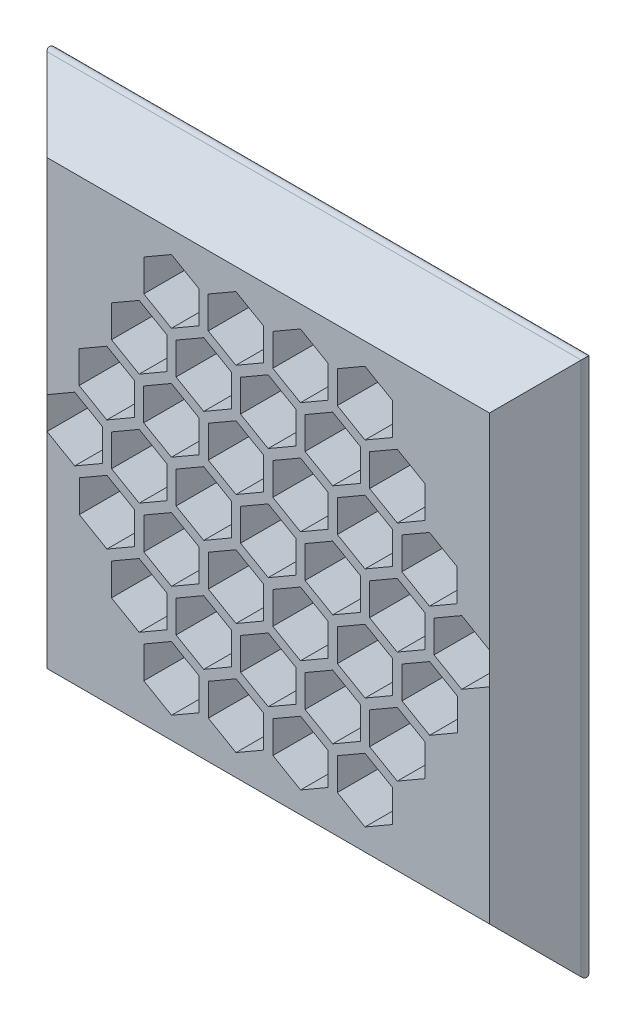
SolidWorks part; units mm, degrees
ref_plane "Front Plane" through (0, 0, 0) normal (0, 0, 1) x (1, 0, 0)
ref_plane "Top Plane" through (0, 0, 0) normal (0, 1, 0) x (1, 0, 0)
ref_plane "Right Plane" through (0, 0, 0) normal (1, 0, 0) x (0, 0, -1)
sketch "Sketch1" plane through (0, 0, 0) normal (0, 0, 1) x (1, 0, 0)
  line L1 (-50, -50) -> (50, -50)
  line L2 (-50, -50) -> (-50, 50)
  line L3 (-50, 50) -> (50, 50)
  line L4 (50, -50) -> (50, 50)
  line L5 (-50, -50) -> (50, 50) construction
  line L6 (-50, 50) -> (50, -50) construction
  point P0 (0, 0)
extrude "Boss-Extrude1" add sketch "Sketch1" along normal blind 10 draft 45
fillet "Fillet1" radius 1 4 edges at (0, 50, 0) (-50, 0, 0) (0, -50, 0) (50, 0, 0)
sketch "Sketch3" plane through (0, 0, 0) normal (0, 0, -1) x (-1, 0, 0)
  line L7 (-35, -35) -> (35, -35) construction
  line L8 (-35, -35) -> (-35, 35) construction
  line L9 (-35, 35) -> (35, 35) construction
  line L10 (35, -35) -> (35, 35) construction
  line L11 (-35, -35) -> (35, 35) construction
  line L12 (-35, 35) -> (35, -35) construction
  line L66 (11.66, -5.7735) -> (16.66, -2.8868)
  line L67 (0, -5.7735) -> (5, -2.8868)
  line L68 (5, -2.8868) -> (5, 2.8868)
  line L69 (5, 2.8868) -> (0, 5.7735)
  line L70 (0, 5.7735) -> (-5, 2.8868)
  line L71 (-5, 2.8868) -> (-5, -2.8868)
  line L72 (-5, -2.8868) -> (0, -5.7735)
  line L73 (16.66, -2.8868) -> (16.66, 2.8868)
  line L74 (16.66, 2.8868) -> (11.66, 5.7735)
  line L75 (11.66, 5.7735) -> (6.66, 2.8868)
  line L76 (6.66, 2.8868) -> (6.66, -2.8868)
  line L77 (6.66, -2.8868) -> (11.66, -5.7735)
  line L78 (23.32, -5.7735) -> (28.32, -2.8868)
  line L79 (28.32, -2.8868) -> (28.32, 2.8868)
  line L80 (28.32, 2.8868) -> (23.32, 5.7735)
  line L81 (23.32, 5.7735) -> (18.32, 2.8868)
  line L82 (18.32, 2.8868) -> (18.32, -2.8868)
  line L83 (18.32, -2.8868) -> (23.32, -5.7735)
  line L84 (34.98, -5.7735) -> (39.98, -2.8868)
  line L85 (39.98, -2.8868) -> (39.98, 2.8868)
  line L86 (39.98, 2.8868) -> (34.98, 5.7735)
  line L87 (34.98, 5.7735) -> (29.98, 2.8868)
  line L88 (29.98, 2.8868) -> (29.98, -2.8868)
  line L89 (29.98, -2.8868) -> (34.98, -5.7735)
  line L90 (-5, -2.8868) -> (0, -5.7735)
  line L91 (0, -5.7735) -> (5, -2.8868)
  line L92 (5, -2.8868) -> (5, 2.8868)
  line L93 (5, 2.8868) -> (0, 5.7735)
  line L94 (0, 5.7735) -> (-5, 2.8868)
  line L95 (-5, 2.8868) -> (-5, -2.8868)
  line L96 (0.83, -12.9846) -> (5.83, -15.8714)
  line L97 (5.83, -15.8714) -> (10.83, -12.9846)
  line L98 (10.83, -12.9846) -> (10.83, -7.2111)
  line L99 (10.83, -7.2111) -> (5.83, -4.3244)
  line L100 (5.83, -4.3244) -> (0.83, -7.2111)
  line L101 (0.83, -7.2111) -> (0.83, -12.9846)
  line L102 (6.66, -23.0825) -> (11.66, -25.9692)
  line L103 (11.66, -25.9692) -> (16.66, -23.0825)
  line L104 (16.66, -23.0825) -> (16.66, -17.309)
  line L105 (16.66, -17.309) -> (11.66, -14.4222)
  line L106 (11.66, -14.4222) -> (6.66, -17.309)
  line L107 (6.66, -17.309) -> (6.66, -23.0825)
  line L108 (12.49, -33.1803) -> (17.49, -36.0671)
  line L109 (17.49, -36.0671) -> (22.49, -33.1803)
  line L110 (22.49, -33.1803) -> (22.49, -27.4068)
  line L111 (22.49, -27.4068) -> (17.49, -24.5201)
  line L112 (17.49, -24.5201) -> (12.49, -27.4068)
  line L113 (12.49, -27.4068) -> (12.49, -33.1803)
  line L114 (-5, 2.8868) -> (-5, -2.8868)
  line L115 (-5, -2.8868) -> (0, -5.7735)
  line L116 (0, -5.7735) -> (5, -2.8868)
  line L117 (5, -2.8868) -> (5, 2.8868)
  line L118 (5, 2.8868) -> (0, 5.7735)
  line L119 (0, 5.7735) -> (-5, 2.8868)
  line L120 (-10.83, -7.2111) -> (-10.83, -12.9846)
  line L121 (-10.83, -12.9846) -> (-5.83, -15.8714)
  line L122 (-5.83, -15.8714) -> (-0.83, -12.9846)
  line L123 (-0.83, -12.9846) -> (-0.83, -7.2111)
  line L124 (-0.83, -7.2111) -> (-5.83, -4.3244)
  line L125 (-5.83, -4.3244) -> (-10.83, -7.2111)
  line L126 (-16.66, -17.309) -> (-16.66, -23.0825)
  line L127 (-16.66, -23.0825) -> (-11.66, -25.9692)
  line L128 (-11.66, -25.9692) -> (-6.66, -23.0825)
  line L129 (-6.66, -23.0825) -> (-6.66, -17.309)
  line L130 (-6.66, -17.309) -> (-11.66, -14.4222)
  line L131 (-11.66, -14.4222) -> (-16.66, -17.309)
  line L132 (-22.49, -27.4068) -> (-22.49, -33.1803)
  line L133 (-22.49, -33.1803) -> (-17.49, -36.0671)
  line L134 (-17.49, -36.0671) -> (-12.49, -33.1803)
  line L135 (-12.49, -33.1803) -> (-12.49, -27.4068)
  line L136 (-12.49, -27.4068) -> (-17.49, -24.5201)
  line L137 (-17.49, -24.5201) -> (-22.49, -27.4068)
  line L138 (0, 5.7735) -> (-5, 2.8868)
  line L139 (-5, 2.8868) -> (-5, -2.8868)
  line L140 (-5, -2.8868) -> (0, -5.7735)
  line L141 (0, -5.7735) -> (5, -2.8868)
  line L142 (5, -2.8868) -> (5, 2.8868)
  line L143 (5, 2.8868) -> (0, 5.7735)
  line L144 (-11.66, 5.7735) -> (-16.66, 2.8868)
  line L145 (-16.66, 2.8868) -> (-16.66, -2.8868)
  line L146 (-16.66, -2.8868) -> (-11.66, -5.7735)
  line L147 (-11.66, -5.7735) -> (-6.66, -2.8868)
  line L148 (-6.66, -2.8868) -> (-6.66, 2.8868)
  line L149 (-6.66, 2.8868) -> (-11.66, 5.7735)
  line L150 (-23.32, 5.7735) -> (-28.32, 2.8868)
  line L151 (-28.32, 2.8868) -> (-28.32, -2.8868)
  line L152 (-28.32, -2.8868) -> (-23.32, -5.7735)
  line L153 (-23.32, -5.7735) -> (-18.32, -2.8868)
  line L154 (-18.32, -2.8868) -> (-18.32, 2.8868)
  line L155 (-18.32, 2.8868) -> (-23.32, 5.7735)
  line L156 (-34.98, 5.7735) -> (-39.98, 2.8868)
  line L157 (-39.98, 2.8868) -> (-39.98, -2.8868)
  line L158 (-39.98, -2.8868) -> (-34.98, -5.7735)
  line L159 (-34.98, -5.7735) -> (-29.98, -2.8868)
  line L160 (-29.98, -2.8868) -> (-29.98, 2.8868)
  line L161 (-29.98, 2.8868) -> (-34.98, 5.7735)
  line L162 (5, 2.8868) -> (0, 5.7735)
  line L163 (0, 5.7735) -> (-5, 2.8868)
  line L164 (-5, 2.8868) -> (-5, -2.8868)
  line L165 (-5, -2.8868) -> (0, -5.7735)
  line L166 (0, -5.7735) -> (5, -2.8868)
  line L167 (5, -2.8868) -> (5, 2.8868)
  line L168 (-0.83, 12.9846) -> (-5.83, 15.8714)
  line L169 (-5.83, 15.8714) -> (-10.83, 12.9846)
  line L170 (-10.83, 12.9846) -> (-10.83, 7.2111)
  line L171 (-10.83, 7.2111) -> (-5.83, 4.3244)
  line L172 (-5.83, 4.3244) -> (-0.83, 7.2111)
  line L173 (-0.83, 7.2111) -> (-0.83, 12.9846)
  line L174 (-6.66, 23.0825) -> (-11.66, 25.9692)
  line L175 (-11.66, 25.9692) -> (-16.66, 23.0825)
  line L176 (-16.66, 23.0825) -> (-16.66, 17.309)
  line L177 (-16.66, 17.309) -> (-11.66, 14.4222)
  line L178 (-11.66, 14.4222) -> (-6.66, 17.309)
  line L179 (-6.66, 17.309) -> (-6.66, 23.0825)
  line L180 (-12.49, 33.1803) -> (-17.49, 36.0671)
  line L181 (-17.49, 36.0671) -> (-22.49, 33.1803)
  line L182 (-22.49, 33.1803) -> (-22.49, 27.4068)
  line L183 (-22.49, 27.4068) -> (-17.49, 24.5201)
  line L184 (-17.49, 24.5201) -> (-12.49, 27.4068)
  line L185 (-12.49, 27.4068) -> (-12.49, 33.1803)
  line L186 (5, -2.8868) -> (5, 2.8868)
  line L187 (5, 2.8868) -> (0, 5.7735)
  line L188 (0, 5.7735) -> (-5, 2.8868)
  line L189 (-5, 2.8868) -> (-5, -2.8868)
  line L190 (-5, -2.8868) -> (0, -5.7735)
  line L191 (0, -5.7735) -> (5, -2.8868)
  line L192 (10.83, 7.2111) -> (10.83, 12.9846)
  line L193 (10.83, 12.9846) -> (5.83, 15.8714)
  line L194 (5.83, 15.8714) -> (0.83, 12.9846)
  line L195 (0.83, 12.9846) -> (0.83, 7.2111)
  line L196 (0.83, 7.2111) -> (5.83, 4.3244)
  line L197 (5.83, 4.3244) -> (10.83, 7.2111)
  line L198 (16.66, 17.309) -> (16.66, 23.0825)
  line L199 (16.66, 23.0825) -> (11.66, 25.9692)
  line L200 (11.66, 25.9692) -> (6.66, 23.0825)
  line L201 (6.66, 23.0825) -> (6.66, 17.309)
  line L202 (6.66, 17.309) -> (11.66, 14.4222)
  line L203 (11.66, 14.4222) -> (16.66, 17.309)
  line L204 (22.49, 27.4068) -> (22.49, 33.1803)
  line L205 (22.49, 33.1803) -> (17.49, 36.0671)
  line L206 (17.49, 36.0671) -> (12.49, 33.1803)
  line L207 (12.49, 33.1803) -> (12.49, 27.4068)
  line L208 (12.49, 27.4068) -> (17.49, 24.5201)
  line L209 (17.49, 24.5201) -> (22.49, 27.4068)
  line L210 (22.5056, 7.2111) -> (22.5056, 12.9846)
  line L217 (22.5056, 12.9846) -> (17.5056, 15.8714)
  line L218 (17.5056, 15.8714) -> (12.5056, 12.9846)
  line L219 (12.5056, 12.9846) -> (12.5056, 7.2111)
  line L220 (12.5056, 7.2111) -> (17.5056, 4.3244)
  line L221 (17.5056, 4.3244) -> (22.5056, 7.2111)
  line L222 (34.1812, 7.2111) -> (34.1812, 12.9846)
  line L223 (34.1812, 12.9846) -> (29.1812, 15.8714)
  line L224 (29.1812, 15.8714) -> (24.1812, 12.9846)
  line L225 (24.1812, 12.9846) -> (24.1812, 7.2111)
  line L226 (24.1812, 7.2111) -> (29.1812, 4.3244)
  line L227 (29.1812, 4.3244) -> (34.1812, 7.2111)
  line L228 (23.3356, -25.9962) -> (28.3356, -23.1094)
  line L229 (28.3356, -23.1094) -> (28.3356, -17.3359)
  line L230 (28.3356, -17.3359) -> (23.3356, -14.4492)
  line L231 (23.3356, -14.4492) -> (18.3356, -17.3359)
  line L232 (18.3356, -17.3359) -> (18.3356, -23.1094)
  line L233 (18.3356, -23.1094) -> (23.3356, -25.9962)
  line L234 (17.4978, -15.8849) -> (22.4978, -12.9981)
  line L235 (22.4978, -12.9981) -> (22.4978, -7.2246)
  line L236 (22.4978, -7.2246) -> (17.4978, -4.3378)
  line L237 (17.4978, -4.3378) -> (12.4978, -7.2246)
  line L238 (12.4978, -7.2246) -> (12.4978, -12.9981)
  line L239 (12.4978, -12.9981) -> (17.4978, -15.8849)
  line L240 (-10.8456, -33.2073) -> (-5.8456, -36.0941)
  line L241 (-5.8456, -36.0941) -> (-0.8456, -33.2073)
  line L242 (-0.8456, -33.2073) -> (-0.8456, -27.4338)
  line L243 (-0.8456, -27.4338) -> (-5.8456, -24.5471)
  line L244 (-5.8456, -24.5471) -> (-10.8456, -27.4338)
  line L245 (-10.8456, -27.4338) -> (-10.8456, -33.2073)
  line L246 (-5.0078, -23.096) -> (-0.0078, -25.9827)
  line L247 (-0.0078, -25.9827) -> (4.9922, -23.096)
  line L248 (4.9922, -23.096) -> (4.9922, -17.3225)
  line L249 (4.9922, -17.3225) -> (-0.0078, -14.4357)
  line L250 (-0.0078, -14.4357) -> (-5.0078, -17.3225)
  line L251 (-5.0078, -17.3225) -> (-5.0078, -23.096)
  line L252 (-34.1812, -7.2111) -> (-34.1812, -12.9846)
  line L253 (-34.1812, -12.9846) -> (-29.1812, -15.8714)
  line L254 (-29.1812, -15.8714) -> (-24.1812, -12.9846)
  line L255 (-24.1812, -12.9846) -> (-24.1812, -7.2111)
  line L256 (-24.1812, -7.2111) -> (-29.1812, -4.3244)
  line L257 (-29.1812, -4.3244) -> (-34.1812, -7.2111)
  line L258 (-22.5056, -7.2111) -> (-22.5056, -12.9846)
  line L259 (-22.5056, -12.9846) -> (-17.5056, -15.8714)
  line L260 (-17.5056, -15.8714) -> (-12.5056, -12.9846)
  line L261 (-12.5056, -12.9846) -> (-12.5056, -7.2111)
  line L262 (-12.5056, -7.2111) -> (-17.5056, -4.3244)
  line L263 (-17.5056, -4.3244) -> (-22.5056, -7.2111)
  line L264 (-23.3356, 25.9962) -> (-28.3356, 23.1094)
  line L265 (-28.3356, 23.1094) -> (-28.3356, 17.3359)
  line L266 (-28.3356, 17.3359) -> (-23.3356, 14.4492)
  line L267 (-23.3356, 14.4492) -> (-18.3356, 17.3359)
  line L268 (-18.3356, 17.3359) -> (-18.3356, 23.1094)
  line L269 (-18.3356, 23.1094) -> (-23.3356, 25.9962)
  line L270 (-17.4978, 15.8849) -> (-22.4978, 12.9981)
  line L271 (-22.4978, 12.9981) -> (-22.4978, 7.2246)
  line L272 (-22.4978, 7.2246) -> (-17.4978, 4.3378)
  line L273 (-17.4978, 4.3378) -> (-12.4978, 7.2246)
  line L274 (-12.4978, 7.2246) -> (-12.4978, 12.9981)
  line L275 (-12.4978, 12.9981) -> (-17.4978, 15.8849)
  line L276 (10.8456, 33.2073) -> (5.8456, 36.0941)
  line L277 (5.8456, 36.0941) -> (0.8456, 33.2073)
  line L278 (0.8456, 33.2073) -> (0.8456, 27.4338)
  line L279 (0.8456, 27.4338) -> (5.8456, 24.5471)
  line L280 (5.8456, 24.5471) -> (10.8456, 27.4338)
  line L281 (10.8456, 27.4338) -> (10.8456, 33.2073)
  line L282 (5.0078, 23.096) -> (0.0078, 25.9827)
  line L283 (0.0078, 25.9827) -> (-4.9922, 23.096)
  line L284 (-4.9922, 23.096) -> (-4.9922, 17.3225)
  line L285 (-4.9922, 17.3225) -> (0.0078, 14.4357)
  line L286 (0.0078, 14.4357) -> (5.0078, 17.3225)
  line L287 (5.0078, 17.3225) -> (5.0078, 23.096)
  line L288 (28.33, 17.309) -> (28.33, 23.0825)
  line L289 (28.33, 23.0825) -> (23.33, 25.9692)
  line L290 (23.33, 25.9692) -> (18.33, 23.0825)
  line L291 (18.33, 23.0825) -> (18.33, 17.309)
  line L292 (18.33, 17.309) -> (23.33, 14.4222)
  line L293 (23.33, 14.4222) -> (28.33, 17.309)
  line L294 (29.155, -15.88) -> (34.155, -12.9933)
  line L295 (34.155, -12.9933) -> (34.155, -7.2198)
  line L296 (34.155, -7.2198) -> (29.155, -4.333)
  line L297 (29.155, -4.333) -> (24.155, -7.2198)
  line L298 (24.155, -7.2198) -> (24.155, -12.9933)
  line L299 (24.155, -12.9933) -> (29.155, -15.88)
  line L300 (0.825, -33.189) -> (5.825, -36.0757)
  line L301 (5.825, -36.0757) -> (10.825, -33.189)
  line L302 (10.825, -33.189) -> (10.825, -27.4155)
  line L303 (10.825, -27.4155) -> (5.825, -24.5287)
  line L304 (5.825, -24.5287) -> (0.825, -27.4155)
  line L305 (0.825, -27.4155) -> (0.825, -33.189)
  line L306 (-28.33, -17.309) -> (-28.33, -23.0825)
  line L307 (-28.33, -23.0825) -> (-23.33, -25.9692)
  line L308 (-23.33, -25.9692) -> (-18.33, -23.0825)
  line L309 (-18.33, -23.0825) -> (-18.33, -17.309)
  line L310 (-18.33, -17.309) -> (-23.33, -14.4222)
  line L311 (-23.33, -14.4222) -> (-28.33, -17.309)
  line L312 (-29.155, 15.88) -> (-34.155, 12.9933)
  line L313 (-34.155, 12.9933) -> (-34.155, 7.2198)
  line L314 (-34.155, 7.2198) -> (-29.155, 4.333)
  line L315 (-29.155, 4.333) -> (-24.155, 7.2198)
  line L316 (-24.155, 7.2198) -> (-24.155, 12.9933)
  line L317 (-24.155, 12.9933) -> (-29.155, 15.88)
  line L318 (-0.825, 33.189) -> (-5.825, 36.0757)
  line L319 (-5.825, 36.0757) -> (-10.825, 33.189)
  line L320 (-10.825, 33.189) -> (-10.825, 27.4155)
  line L321 (-10.825, 27.4155) -> (-5.825, 24.5287)
  line L322 (-5.825, 24.5287) -> (-0.825, 27.4155)
  line L323 (-0.825, 27.4155) -> (-0.825, 33.189)
  line L324 (-6.66, 43.7495) -> (-11.66, 46.6362)
  line L325 (-11.66, 46.6362) -> (-16.66, 43.7495)
  line L326 (-16.66, 43.7495) -> (-16.66, 37.976)
  line L327 (-16.66, 37.976) -> (-11.66, 35.0892)
  line L328 (-11.66, 35.0892) -> (-6.66, 37.976)
  line L329 (-6.66, 37.976) -> (-6.66, 43.7495)
  line L330 (5.0078, 43.763) -> (0.0078, 46.6497)
  line L331 (0.0078, 46.6497) -> (-4.9922, 43.763)
  line L332 (-4.9922, 43.763) -> (-4.9922, 37.9895)
  line L333 (-4.9922, 37.9895) -> (0.0078, 35.1027)
  line L334 (0.0078, 35.1027) -> (5.0078, 37.9895)
  line L335 (5.0078, 37.9895) -> (5.0078, 43.763)
  line L336 (16.66, 37.976) -> (16.66, 43.7495)
  line L337 (16.66, 43.7495) -> (11.66, 46.6362)
  line L338 (11.66, 46.6362) -> (6.66, 43.7495)
  line L339 (6.66, 43.7495) -> (6.66, 37.976)
  line L340 (6.66, 37.976) -> (11.66, 35.0892)
  line L341 (11.66, 35.0892) -> (16.66, 37.976)
  line L342 (34.5581, 27.6425) -> (34.5581, 33.416)
  line L343 (34.5581, 33.416) -> (29.5581, 36.3027)
  line L344 (29.5581, 36.3027) -> (24.5581, 33.416)
  line L345 (24.5581, 33.416) -> (24.5581, 27.6425)
  line L346 (24.5581, 27.6425) -> (29.5581, 24.7557)
  line L347 (29.5581, 24.7557) -> (34.5581, 27.6425)
  line L348 (40.4037, 17.5446) -> (40.4037, 23.3181)
  line L349 (40.4037, 23.3181) -> (35.4037, 26.2049)
  line L350 (35.4037, 26.2049) -> (30.4037, 23.3181)
  line L351 (30.4037, 23.3181) -> (30.4037, 17.5446)
  line L352 (30.4037, 17.5446) -> (35.4037, 14.6579)
  line L353 (35.4037, 14.6579) -> (40.4037, 17.5446)
  line L354 (41.2181, 4.56) -> (46.2181, 7.4467)
  line L355 (46.2181, 7.4467) -> (46.2181, 13.2203)
  line L356 (46.2181, 13.2203) -> (41.2181, 16.107)
  line L357 (41.2181, 16.107) -> (36.2181, 13.2203)
  line L358 (36.2181, 13.2203) -> (36.2181, 7.4467)
  line L359 (36.2181, 7.4467) -> (41.2181, 4.56)
  line L360 (41.2181, -16.107) -> (46.2181, -13.2203)
  line L361 (46.2181, -13.2203) -> (46.2181, -7.4467)
  line L362 (46.2181, -7.4467) -> (41.2181, -4.56)
  line L363 (41.2181, -4.56) -> (36.2181, -7.4467)
  line L364 (36.2181, -7.4467) -> (36.2181, -13.2203)
  line L365 (36.2181, -13.2203) -> (41.2181, -16.107)
  line L366 (35.3959, -26.2184) -> (40.3959, -23.3316)
  line L367 (40.3959, -23.3316) -> (40.3959, -17.5581)
  line L368 (40.3959, -17.5581) -> (35.3959, -14.6713)
  line L369 (35.3959, -14.6713) -> (30.3959, -17.5581)
  line L370 (30.3959, -17.5581) -> (30.3959, -23.3316)
  line L371 (30.3959, -23.3316) -> (35.3959, -26.2184)
  line L372 (24.5581, -33.416) -> (29.5581, -36.3027)
  line L373 (29.5581, -36.3027) -> (34.5581, -33.416)
  line L374 (34.5581, -33.416) -> (34.5581, -27.6425)
  line L375 (34.5581, -27.6425) -> (29.5581, -24.7557)
  line L376 (29.5581, -24.7557) -> (24.5581, -27.6425)
  line L377 (24.5581, -27.6425) -> (24.5581, -33.416)
  line L378 (6.66, -43.7495) -> (11.66, -46.6362)
  line L379 (11.66, -46.6362) -> (16.66, -43.7495)
  line L380 (16.66, -43.7495) -> (16.66, -37.976)
  line L381 (16.66, -37.976) -> (11.66, -35.0892)
  line L382 (11.66, -35.0892) -> (6.66, -37.976)
  line L383 (6.66, -37.976) -> (6.66, -43.7495)
  line L384 (-5.0078, -43.763) -> (-0.0078, -46.6497)
  line L385 (-0.0078, -46.6497) -> (4.9922, -43.763)
  line L386 (4.9922, -43.763) -> (4.9922, -37.9895)
  line L387 (4.9922, -37.9895) -> (-0.0078, -35.1027)
  line L388 (-0.0078, -35.1027) -> (-5.0078, -37.9895)
  line L389 (-5.0078, -37.9895) -> (-5.0078, -43.763)
  line L390 (-16.66, -37.976) -> (-16.66, -43.7495)
  line L391 (-16.66, -43.7495) -> (-11.66, -46.6362)
  line L392 (-11.66, -46.6362) -> (-6.66, -43.7495)
  line L393 (-6.66, -43.7495) -> (-6.66, -37.976)
  line L394 (-6.66, -37.976) -> (-11.66, -35.0892)
  line L395 (-11.66, -35.0892) -> (-16.66, -37.976)
  line L396 (-34.5581, -27.6425) -> (-34.5581, -33.416)
  line L397 (-34.5581, -33.416) -> (-29.5581, -36.3027)
  line L398 (-29.5581, -36.3027) -> (-24.5581, -33.416)
  line L399 (-24.5581, -33.416) -> (-24.5581, -27.6425)
  line L400 (-24.5581, -27.6425) -> (-29.5581, -24.7557)
  line L401 (-29.5581, -24.7557) -> (-34.5581, -27.6425)
  line L402 (-40.4037, -17.5446) -> (-40.4037, -23.3181)
  line L403 (-40.4037, -23.3181) -> (-35.4037, -26.2049)
  line L404 (-35.4037, -26.2049) -> (-30.4037, -23.3181)
  line L405 (-30.4037, -23.3181) -> (-30.4037, -17.5446)
  line L406 (-30.4037, -17.5446) -> (-35.4037, -14.6579)
  line L407 (-35.4037, -14.6579) -> (-40.4037, -17.5446)
  line L408 (-41.2181, -4.56) -> (-46.2181, -7.4467)
  line L409 (-46.2181, -7.4467) -> (-46.2181, -13.2203)
  line L410 (-46.2181, -13.2203) -> (-41.2181, -16.107)
  line L411 (-41.2181, -16.107) -> (-36.2181, -13.2203)
  line L412 (-36.2181, -13.2203) -> (-36.2181, -7.4467)
  line L413 (-36.2181, -7.4467) -> (-41.2181, -4.56)
  line L414 (-41.2181, 16.107) -> (-46.2181, 13.2203)
  line L415 (-46.2181, 13.2203) -> (-46.2181, 7.4467)
  line L416 (-46.2181, 7.4467) -> (-41.2181, 4.56)
  line L417 (-41.2181, 4.56) -> (-36.2181, 7.4467)
  line L418 (-36.2181, 7.4467) -> (-36.2181, 13.2203)
  line L419 (-36.2181, 13.2203) -> (-41.2181, 16.107)
  line L420 (-35.3959, 26.2184) -> (-40.3959, 23.3316)
  line L421 (-40.3959, 23.3316) -> (-40.3959, 17.5581)
  line L422 (-40.3959, 17.5581) -> (-35.3959, 14.6713)
  line L423 (-35.3959, 14.6713) -> (-30.3959, 17.5581)
  line L424 (-30.3959, 17.5581) -> (-30.3959, 23.3316)
  line L425 (-30.3959, 23.3316) -> (-35.3959, 26.2184)
  line L426 (-24.5581, 33.416) -> (-29.5581, 36.3027)
  line L427 (-29.5581, 36.3027) -> (-34.5581, 33.416)
  line L428 (-34.5581, 33.416) -> (-34.5581, 27.6425)
  line L429 (-34.5581, 27.6425) -> (-29.5581, 24.7557)
  line L430 (-29.5581, 24.7557) -> (-24.5581, 27.6425)
  line L431 (-24.5581, 27.6425) -> (-24.5581, 33.416)
  circle A0 centre (0, 0) radius 5 construction
  point P1 (0, 0)
  point P155 (0, 0)
  point P228 (0, 0)
  point P264 (0, 0)
  point P374 (0, 0)
extrude "Cut-Extrude1" cut sketch "Sketch3" against normal through all contours L184 L185 L180 L181 L182 L183 | L322 L323 L318 L319 L320 L321 | L280 L281 L276 L277 L278 L279 | L208 L209 L204 L205 L206 L207 | L226 L227 L222 L223 L224 L225 | L292 L293 L288 L289 L290 L291 | L202 L203 L198 L199 L200 L201 | L286 L287 L282 L283 L284 L285 | L178 L179 L174 L175 L176 L177 | L268 L269 L264 L265 L266 L267 | L316 L317 L312 L313 L314 L315 | L274 L275 L270 L271 L272 L273 | L172 L173 L168 L169 L170 L171 | L196 L197 L192 L193 L194 L195 | L220 L221 L210 L217 L218 L219 | L82 L83 L78 L79 L80 L81 | L88 L89 L84 L85 L86 L87 | L298 L299 L294 L295 L296 L297 | L238 L239 L234 L235 L236 L237 | L76 L77 L66 L73 L74 L75 | L100 L101 L96 L97 L98 L99 | L148 L149 L144 L145 L146 L147 | L154 L155 L150 L151 L152 L153 | L160 L161 L156 L157 L158 L159 | L256 L257 L252 L253 L254 L255 | L262 L263 L258 L259 L260 L261 | L124 L125 L120 L121 L122 L123 | L106 L107 L102 L103 L104 L105 | L232 L233 L228 L229 L230 L231 | L112 L113 L108 L109 L110 L111 | L136 L137 L132 L133 L134 L135 | L310 L311 L306 L307 L308 L309 | L130 L131 L126 L127 L128 L129 | L250 L251 L246 L247 L248 L249 | L304 L305 L300 L301 L302 L303 | L244 L245 L240 L241 L242 L243 | L67 L68 L69 L70 L71 L72
equation "\"A\"= 100"
equation "\"B\"= 100"
equation "\"C\"= 10"
equation "\"D1@Sketch1\"=\"A\""
equation "\"D2@Sketch1\"=\"B\""
equation "\"D1@Boss-Extrude1\"=\"C\""
equation "\"D2@Sketch3\"=\"Holes Frame\""
equation "\"D3@Sketch3\"=\"Holes Frame\""
equation "\"Holes Frame\"= \"A\" - ( \"A\" * ( 3 / 10 ) )"
equation "\"LED Ø\"= 10"
